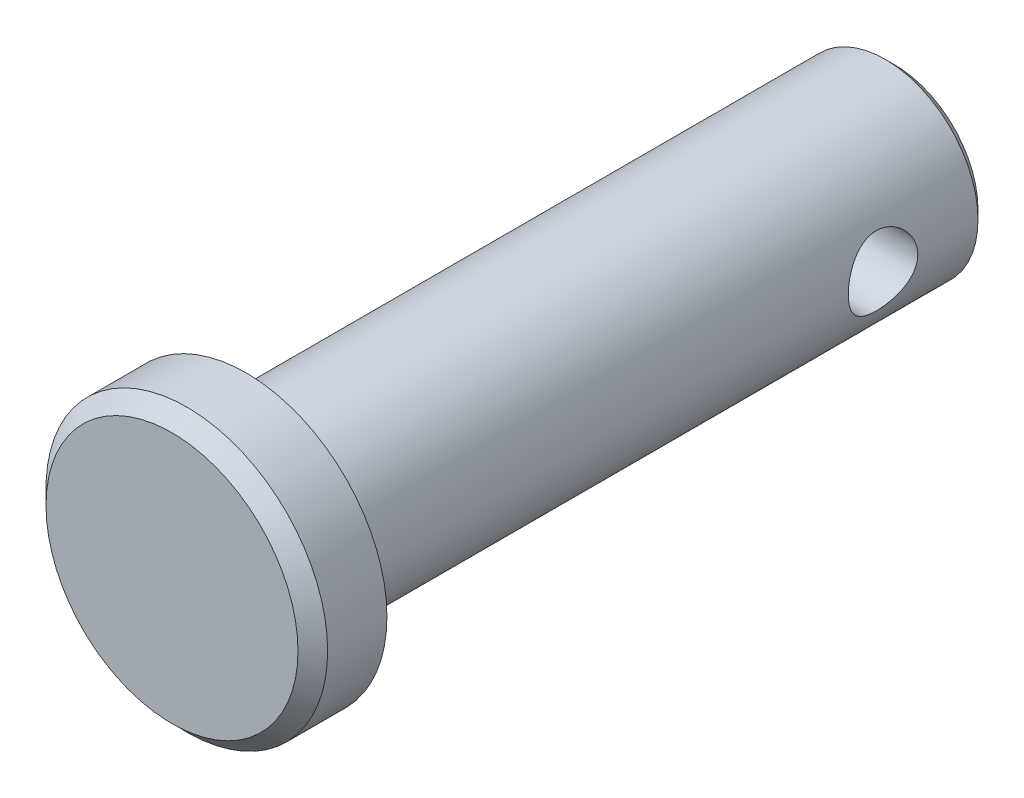
SolidWorks part; units mm, degrees
ref_plane "Front" through (0, 0, 0) normal (0, 0, 1) x (1, 0, 0)
ref_plane "Top" through (0, 0, 0) normal (0, 1, 0) x (1, 0, 0)
ref_plane "Right" through (0, 0, 0) normal (1, 0, 0) x (0, 0, -1)
sketch "Sketch1" plane through (0, 0, 0) normal (0, 0, 1) x (1, 0, 0)
  circle A0 centre (0, 0) radius 3.175
  point P3 (0, 3.175)
  point P4 (0, -3.175)
  dimension "dia" = 6.35
extrude "Extrude1" add sketch "Sketch1" along normal mid plane 22.225
sketch "Sketch2" plane through (0, 0, 11.1125) normal (0, 0, 1) x (1, 0, 0)
  circle A0 centre (0, 0) radius 4.826
  dimension "head dia" = 9.652
extrude "Extrude2" add sketch "Sketch2" along normal blind 2.54
chamfer "Chamfer1" distance 0.508 angle 45 1 edges at (4.826, 0, 13.6525)
sketch "Sketch3" plane through (0, 0, 0) normal (1, 0, 0) x (0, 0, -1)
  line L0 (-11.1125, -3.175) -> (-11.1125, 3.175) construction
  circle A0 centre (7.5406, 0) radius 1.1906
  point P2 (6.35, 0)
  dimension "hole dia" = 2.3813
  dimension "useable Lg" = 17.4625
extrude "Extrude3" cut sketch "Sketch3" against normal through all and the other way through all
chamfer "Chamfer2" distance 0.3175 angle 45 1 edges at (3.175, 0, -11.1125)
ref_plane "Plane1" through (0, 0, -7.5406) normal (0, 0, 1) x (1, 0, 0)
sketch "Sketch8" plane through (0, 0, 0) normal (1, 0, 0) x (0, 0, -1)
  line L0 (-13.6525, 4.318) -> (-13.6525, -4.318) construction
  line L1 (-13.1445, -4.826) -> (-11.1125, -4.826) construction
  line L2 (11.1125, -2.8575) -> (11.1125, 2.8575) construction
  point P0 (-13.6525, 4.826)
  point P1 (-11.1125, 4.826)
  point P5 (11.1125, 3.175)
  point P8 (-13.6525, -4.826)
  point P9 (11.1125, -3.175)
equation "\"D1@Chamfer1\" = \"head ht@Extrude2\" * .2"
equation "\"D1@Chamfer2\" = \"dia@Sketch1\" * .05"
